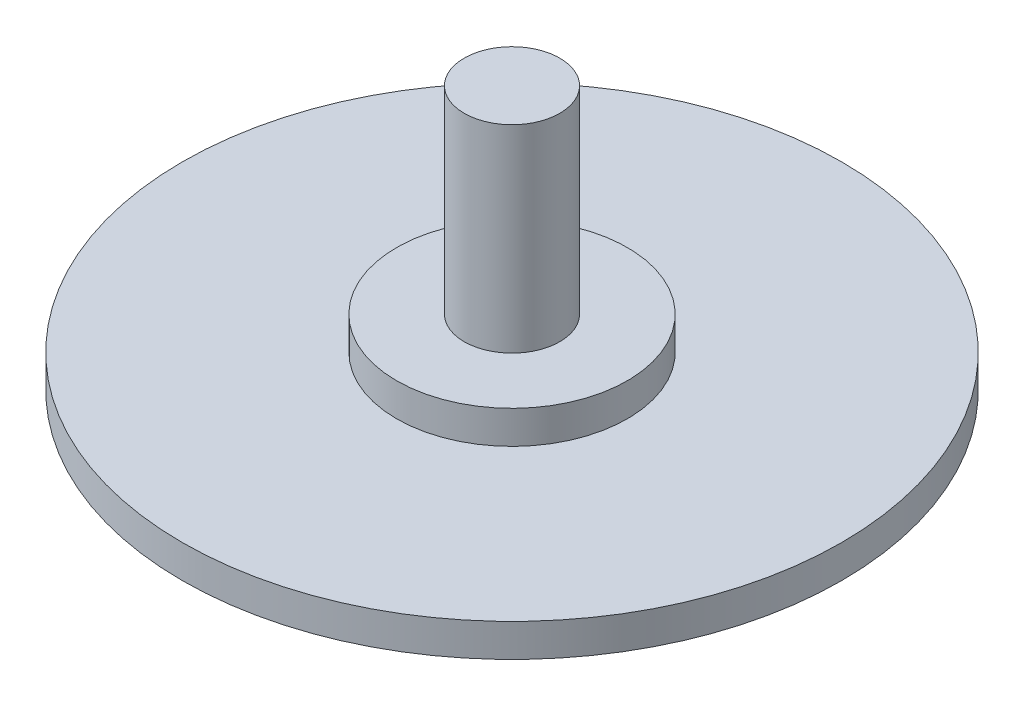
SolidWorks part; units mm, degrees
ref_plane "Plan de face" through (0, 0, 0) normal (0, 0, 1) x (1, 0, 0)
ref_plane "Plan de dessus" through (0, 0, 0) normal (0, 1, 0) x (1, 0, 0)
ref_plane "Plan de droite" through (0, 0, 0) normal (1, 0, 0) x (0, 0, -1)
sketch "Esquisse1" plane through (0, 0, 0) normal (0, 1, 0) x (1, 0, 0)
  circle A0 centre (0, 0) radius 10
  dimension "D1" = 20
extrude "Boss.-Extru.1" add sketch "Esquisse1" along normal blind 1
sketch "Esquisse2" plane through (0, 1, 0) normal (0, 1, 0) x (1, 0, 0)
  circle A0 centre (0, 0) radius 1.45
  dimension "D1" = 2.9
extrude "Boss.-Extru.2" add sketch "Esquisse2" along normal blind 7
sketch "Esquisse3" plane through (0, 1, 0) normal (0, 1, 0) x (1, 0, 0)
  circle A0 centre (0, 0) radius 3.5
  dimension "D1" = 7
extrude "Boss.-Extru.3" add sketch "Esquisse3" along normal blind 1
